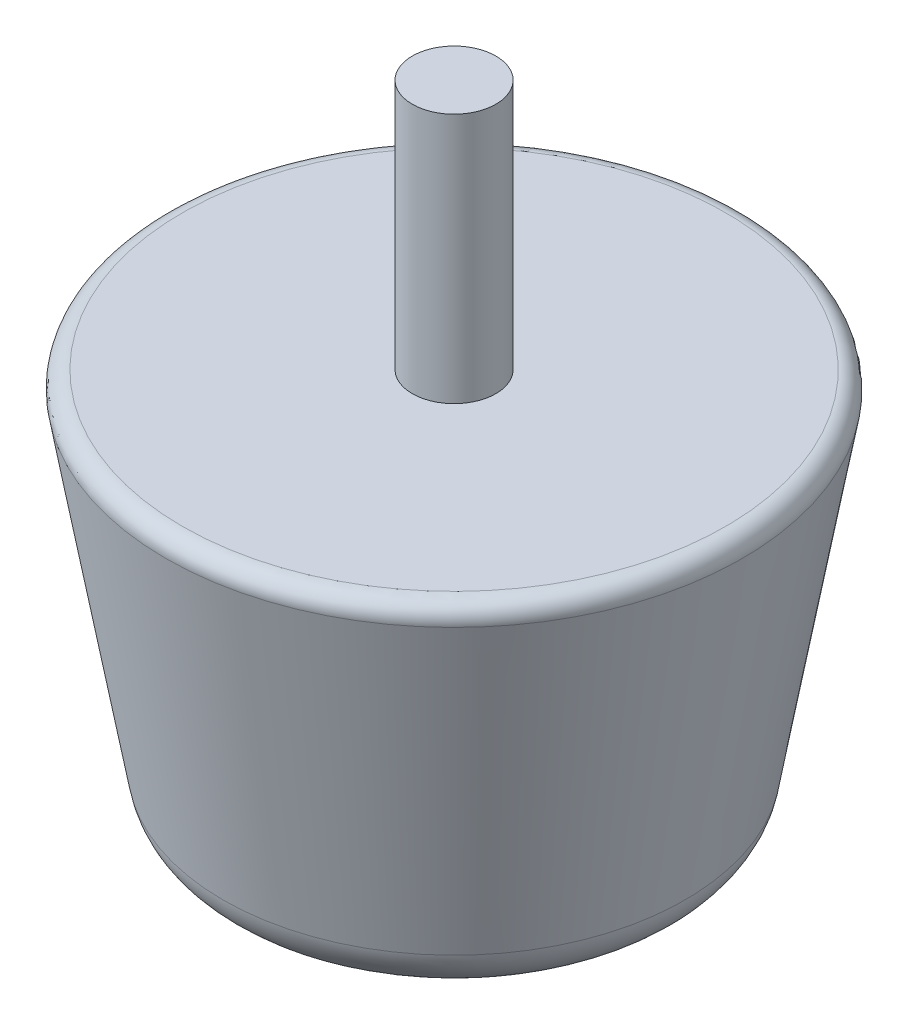
SolidWorks part; units mm, degrees
ref_plane "Front Plane" through (0, 0, 0) normal (0, 0, 1) x (1, 0, 0)
ref_plane "Top Plane" through (0, 0, 0) normal (0, 1, 0) x (1, 0, 0)
ref_plane "Right Plane" through (0, 0, 0) normal (1, 0, 0) x (0, 0, -1)
sketch "Sketch1" plane through (0, 0, 0) normal (0, 1, 0) x (1, 0, 0)
  circle A0 centre (0, 0) radius 40
  dimension "D1" = 80
extrude "Boss-Extrude1" add sketch "Sketch1" along normal blind 70 draft 10 draft outward yes
sketch "Sketch2" plane through (0, 0, 0) normal (1, 0, 0) x (0, 0, -1)
  circle A0 centre (0, 42.2968) radius 9
  dimension "D1" = 18
extrude "Cut-Extrude1" cut sketch "Sketch2" against normal up to next from offset 45 offset against normal yes
sketch "Sketch3" plane through (0, 70, 0) normal (0, 1, 0) x (1, 0, 0)
  circle A0 centre (0, 0) radius 7.5
  dimension "D1" = 15
extrude "Boss-Extrude2" add sketch "Sketch3" along normal blind 45
fillet "Fillet1" radius 10 1 edges at (0, 0, 40)
fillet "Fillet2" radius 3 1 edges at (0, 70, 52.3429)
